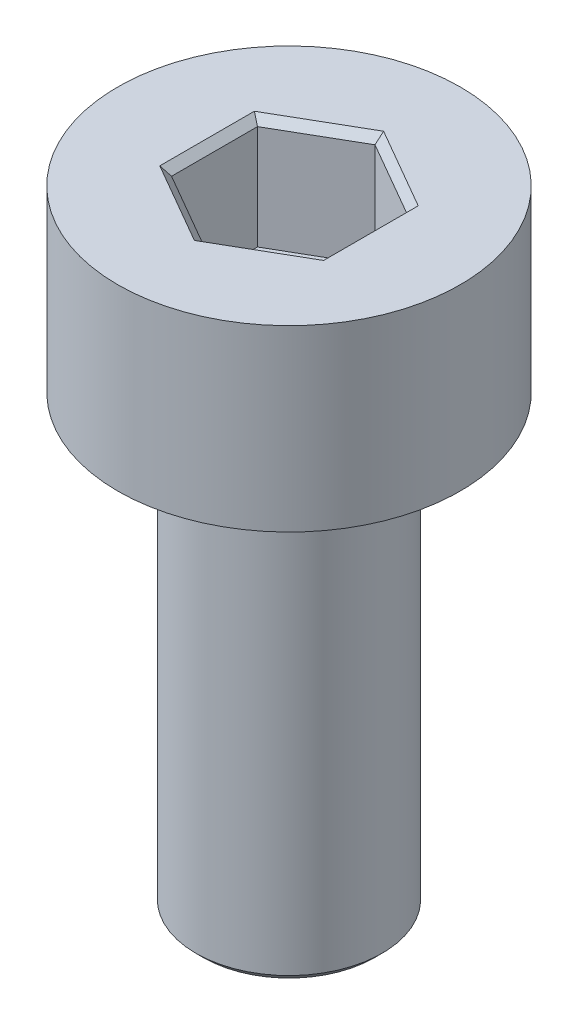
SolidWorks part; units mm, degrees
material "铸造合金钢"
ref_plane "前视基准面" through (0, 0, 0) normal (0, 0, 1) x (1, 0, 0)
ref_plane "上视基准面" through (0, 0, 0) normal (0, 1, 0) x (1, 0, 0)
ref_plane "右视基准面" through (0, 0, 0) normal (1, 0, 0) x (0, 0, -1)
sketch "草图1" plane through (0, 0, 0) normal (0, 1, 0) x (1, 0, 0)
  circle A0 centre (0, 0) radius 2.3
  dimension "D1" = 4.6
extrude "凸台-拉伸1" add sketch "草图1" along normal blind 2.4
sketch "草图2" plane through (0, 2.4, 0) normal (0, 1, 0) x (1, 0, 0)
  line L1 (0, -1.1547) -> (1, -0.5774)
  line L2 (1, -0.5774) -> (1, 0.5774)
  line L3 (1, 0.5774) -> (0, 1.1547)
  line L4 (0, 1.1547) -> (-1, 0.5774)
  line L5 (-1, 0.5774) -> (-1, -0.5774)
  line L6 (-1, -0.5774) -> (0, -1.1547)
  circle A0 centre (0, 0) radius 1 construction
  dimension "D1" = 2
extrude "切除-拉伸1" cut sketch "草图2" against normal blind 1.5
sketch "草图3" plane through (0, 0, 0) normal (0, -1, 0) x (1, 0, 0)
  circle A0 centre (0, 0) radius 1.25
  dimension "D1" = 2.5
extrude "凸台-拉伸2" add sketch "草图3" along normal blind 6
chamfer "倒角1" distance 0.1 angle 45 7 edges at (0.5, 2.4, -0.866) (-0.5, 2.4, -0.866) (-1, 2.4, 0) (-0.5, 2.4, 0.866) (0.5, 2.4, 0.866) (1, 2.4, 0) (0, -6, -1.25)
